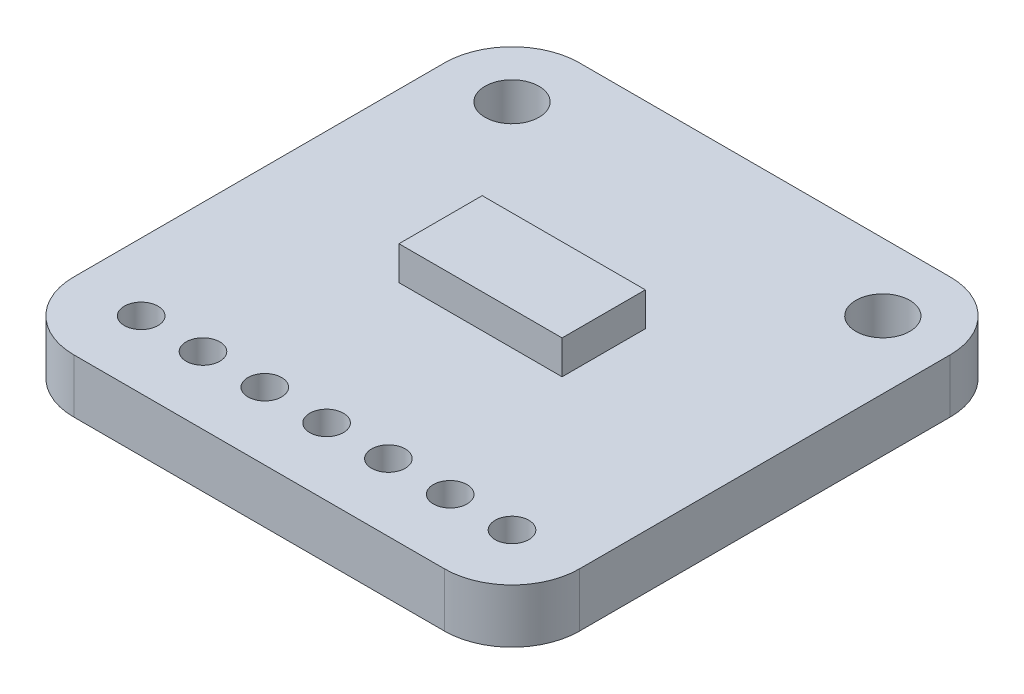
SolidWorks part; units mm, degrees
ref_plane "Front Plane" through (0, 0, 0) normal (0, 0, 1) x (1, 0, 0)
ref_plane "Top Plane" through (0, 0, 0) normal (0, 1, 0) x (1, 0, 0)
ref_plane "Right Plane" through (0, 0, 0) normal (1, 0, 0) x (0, 0, -1)
sketch "Sketch1" plane through (0, 0, 0) normal (0, 1, 0) x (1, 0, 0)
  line L0 (0, 2.54) -> (0, 16.51)
  line L1 (2.54, 19.05) -> (16.51, 19.05)
  line L2 (19.05, 16.51) -> (19.05, 2.54)
  line L3 (16.51, 0) -> (2.54, 0)
  arc A0 (0, 16.51) -> (2.54, 19.05) centre (2.54, 16.51) cw
  arc A1 (16.51, 19.05) -> (19.05, 16.51) centre (16.51, 16.51) cw
  arc A2 (19.05, 2.54) -> (16.51, 0) centre (16.51, 2.54) cw
  arc A3 (0, 2.54) -> (2.54, 0) centre (2.54, 2.54) ccw
  point P13 (0, 0)
  dimension "D1" = 2.54
  dimension "D2" = 19.05
  dimension "D3" = 19.05
extrude "Boss-Extrude1" add sketch "Sketch1" along normal blind 2.032
sketch "Sketch2" plane through (0, 2.032, 0) normal (0, 1, 0) x (1, 0, 0)
  line L0 (2.54, 16.51) -> (16.51, 16.51) construction
  line L1 (16.51, 19.05) -> (2.54, 19.05) construction
  line L2 (2.54, 0) -> (16.51, 0) construction
  line L3 (2.54, 2.54) -> (4.8683, 2.54) construction
  line L4 (4.8683, 2.54) -> (7.1967, 2.54) construction
  line L5 (7.1967, 2.54) -> (9.525, 2.54) construction
  line L6 (9.525, 2.54) -> (11.8533, 2.54) construction
  line L7 (11.8533, 2.54) -> (14.1817, 2.54) construction
  line L8 (14.1817, 2.54) -> (16.51, 2.54) construction
  circle A0 centre (2.54, 16.51) radius 1.016
  circle A1 centre (16.51, 16.51) radius 1.016
  circle A4 centre (2.54, 2.54) radius 0.635
  circle A5 centre (4.8683, 2.54) radius 0.635
  circle A6 centre (7.1967, 2.54) radius 0.635
  circle A7 centre (9.525, 2.54) radius 0.635
  circle A8 centre (11.8533, 2.54) radius 0.635
  circle A9 centre (14.1817, 2.54) radius 0.635
  circle A10 centre (16.51, 2.54) radius 0.635
  point P4 (9.525, 19.05)
  point P7 (9.525, 16.51)
  point P25 (9.525, 0)
  dimension "D2" = 2.032
  dimension "D5" = 1.27
  dimension "D1" = 13.97
  dimension "D3" = 16.51
  dimension "D4" = 2.54
extrude "Cut-Extrude1" cut sketch "Sketch2" against normal through all
sketch "Sketch3" plane through (0, 2.032, 0) normal (0, 1, 0) x (1, 0, 0)
  line L0 (6.3121, 11.6159) -> (6.3121, 8.4795)
  line L1 (6.3121, 8.4795) -> (12.4574, 8.4795)
  line L2 (12.4574, 8.4795) -> (12.4574, 11.6159)
  line L3 (12.4574, 11.6159) -> (6.3121, 11.6159)
extrude "Boss-Extrude2" add sketch "Sketch3" along normal blind 1.27
